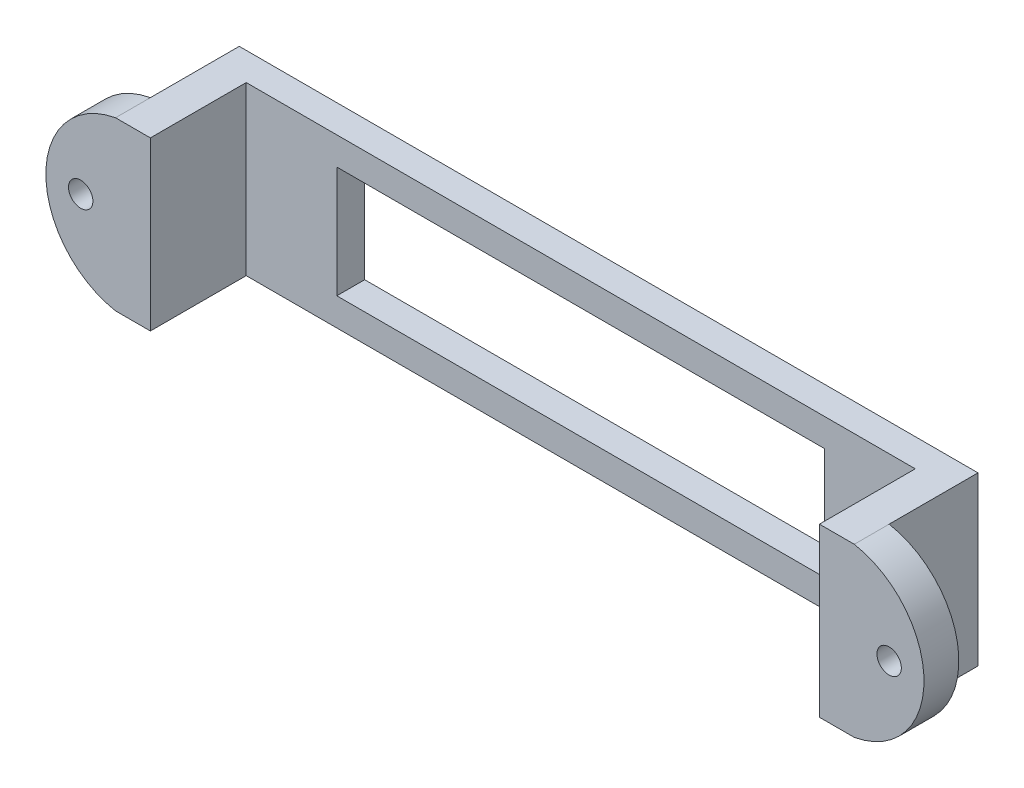
SolidWorks part; units mm, degrees
ref_plane "Plan de face" through (0, 0, 0) normal (0, 0, 1) x (1, 0, 0)
ref_plane "Plan de dessus" through (0, 0, 0) normal (0, 1, 0) x (1, 0, 0)
ref_plane "Plan de droite" through (0, 0, 0) normal (1, 0, 0) x (0, 0, -1)
sketch "Esquisse1" plane through (0, 0, 0) normal (0, 0, 1) x (1, 0, 0)
  line L0 (0, -37.6975) -> (0, 37.6975) construction
  line L1 (-48, 17) -> (48, 17)
  line L2 (-48, 17) -> (-48, -17)
  line L3 (-48, -17) -> (48, -17)
  line L4 (48, 17) -> (48, -17)
  line L5 (-10, 0) -> (10, 0) construction
  line L6 (-35, 8) -> (35, 8)
  line L7 (-53, 12) -> (53, 12)
  line L8 (-53, 12) -> (-53, -12)
  line L9 (-53, -12) -> (53, -12)
  line L10 (53, 12) -> (53, -12)
  line L15 (-35, 8) -> (-35, -8)
  line L16 (-35, -8) -> (35, -8)
  line L17 (35, 8) -> (35, -8)
  point P6 (0, 0)
  point P13 (-48, 0)
  point P14 (48, 0)
  dimension "D1" = 5
  dimension "D2" = 34
  dimension "D3" = 96
  dimension "D4" = 70
  dimension "D5" = 16
  dimension "D6" = 5
extrude "Boss.-Extru.1" add sketch "Esquisse1" along normal blind 4 contours L8 L9 L2 L7 | L2 L9 L4 L7 L6 L17 L16 L15 | L10 L7 L4 L9
sketch "Esquisse2" plane through (0, 0, 4) normal (0, 0, 1) x (1, 0, 0)
  line L0 (-53, -12) -> (53, -12) construction
  line L1 (-53, 12) -> (-48, 12)
  line L2 (-53, 12) -> (-53, -12)
  line L3 (-53, -12) -> (-48, -12)
  line L4 (-48, 12) -> (-48, -12)
  line L5 (0, 12) -> (0, -12) construction
  line L6 (53, 12) -> (48, 12)
  line L7 (53, 12) -> (53, -12)
  line L8 (53, -12) -> (48, -12)
  line L9 (48, 12) -> (48, -12)
  line L10 (-53, 12) -> (53, 12) construction
  dimension "D1" = 5
extrude "Boss.-Extru.2" add sketch "Esquisse2" along normal blind 8.75
sketch "Esquisse3" plane through (0, 0, 12.75) normal (0, 0, 1) x (1, 0, 0)
  line L1 (-48, -12) -> (48, -12) construction
  line L2 (-48, 12) -> (-53, 12)
  line L3 (-48, 12) -> (-48, -12)
  line L4 (-48, -12) -> (-53, -12)
  line L6 (0, 12) -> (0, -12) construction
  line L7 (-48, 12) -> (48, 12) construction
  line L11 (-53, 12) -> (-53, -12) construction
  line L12 (48, -12) -> (53, -12)
  line L13 (48, 12) -> (48, -12)
  line L14 (48, 12) -> (53, 12)
  arc A0 (-53, 12) -> (-53, -12) centre (-50.8, 0) ccw
  arc A1 (53, 12) -> (53, -12) centre (50.8, 0) cw
  point P7 (-63, 0)
  point P21 (63, 0)
  dimension "D1" = 10
extrude "Boss.-Extru.3" add sketch "Esquisse3" along normal blind 5
sketch "Esquisse4" plane through (0, 0, 17.75) normal (0, 0, 1) x (1, 0, 0)
  line L0 (-63, 0) -> (0, 0) construction
  line L1 (0, 12) -> (0, -12) construction
  line L2 (-48, 12) -> (48, 12) construction
  line L3 (-48, -12) -> (48, -12) construction
  circle A0 centre (-58, 0) radius 1.75
  arc A1 (-53, 12) -> (-53, -12) centre (-50.8, 0) ccw construction
  circle A2 centre (58, 0) radius 1.75
  point P2 (-63, 0)
  point P17 (63, 0)
  dimension "D1" = 3.5
  dimension "D2" = 5
extrude "Enlèv. mat.-Extru.2" cut sketch "Esquisse4" against normal through all
ref_plane "Plan1" through (-53, -12, 0) normal (0, -1, 0) x (-1, 0, 0)
